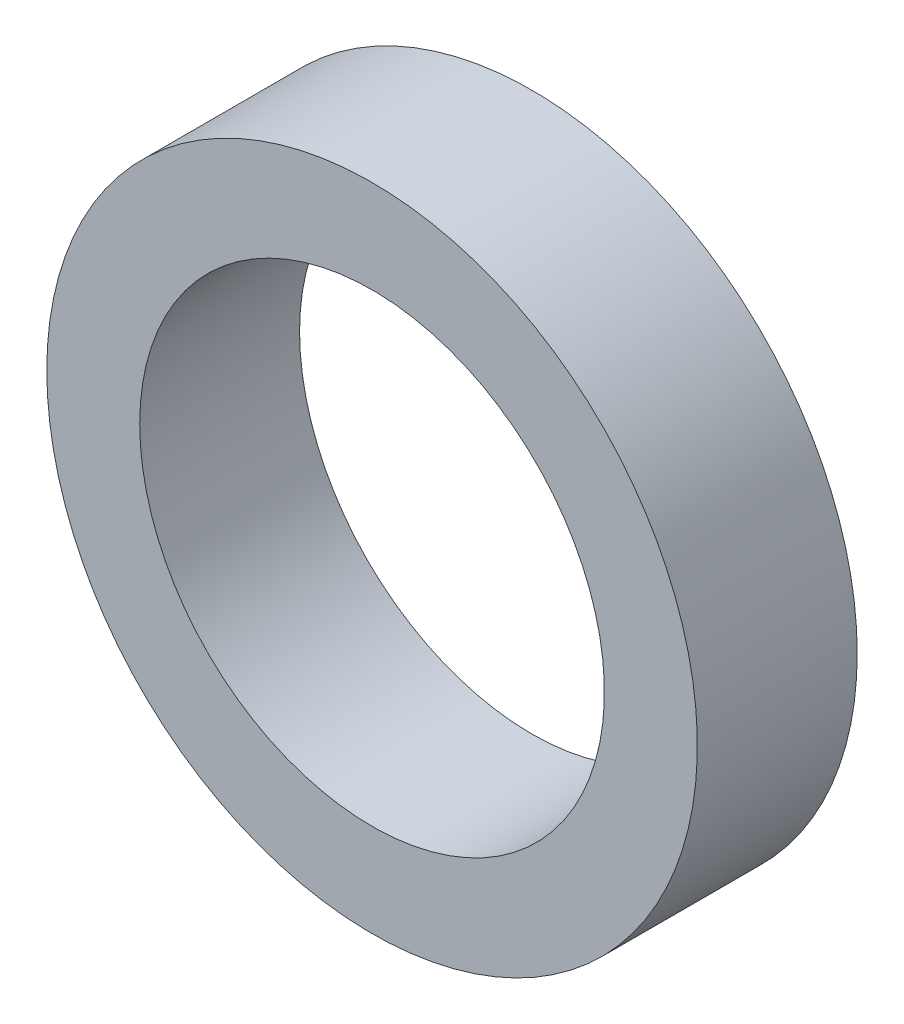
SolidWorks part; units mm, degrees
material "AISI 1020"
ref_plane "Спереди" through (0, 0, 0) normal (0, 0, 1) x (1, 0, 0)
ref_plane "Сверху" through (0, 0, 0) normal (0, 1, 0) x (1, 0, 0)
ref_plane "Справа" through (0, 0, 0) normal (1, 0, 0) x (0, 0, -1)
sketch "Эскиз1" plane through (0, 0, 0) normal (0, 0, 1) x (1, 0, 0)
  circle A0 centre (0, -65) radius 12.5 construction
  circle A1 centre (0, -65) radius 12.5
  circle A2 centre (0, -65) radius 17.5
  dimension "D1" = 5
extrude "Бобышка-Вытянуть1" add sketch "Эскиз1" along normal offset from surface (8.6 mm away) 2
